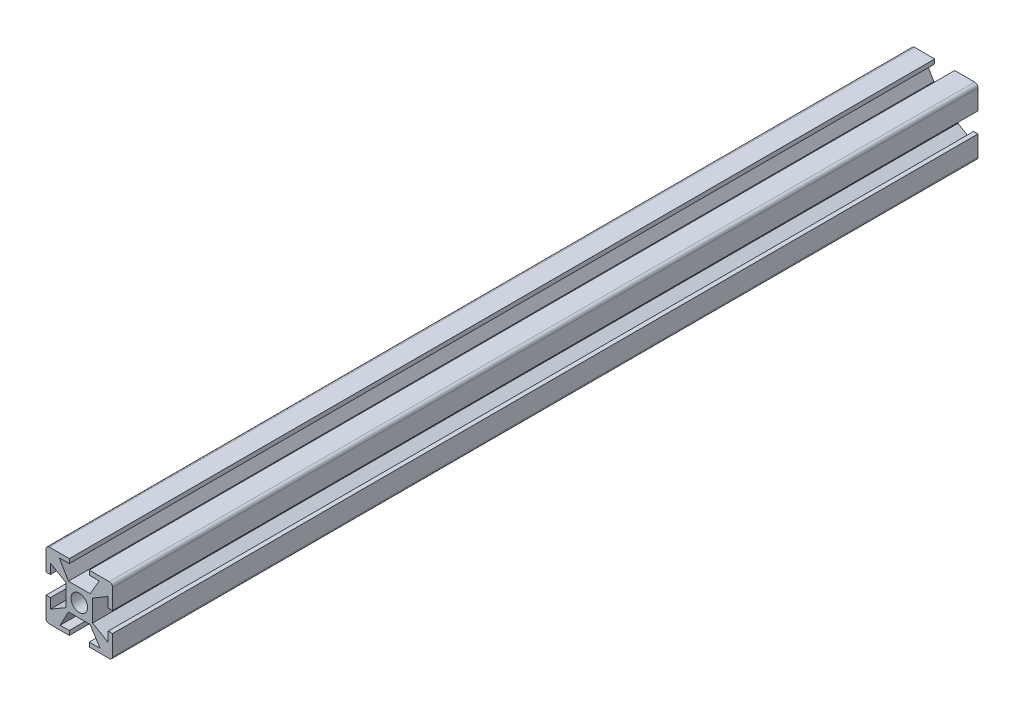
SolidWorks part; units mm, degrees
ref_plane "Alzado" through (0, 0, 0) normal (0, 0, 1) x (1, 0, 0)
ref_plane "Planta" through (0, 0, 0) normal (0, 1, 0) x (1, 0, 0)
ref_plane "Vista lateral" through (0, 0, 0) normal (1, 0, 0) x (0, 0, -1)
sketch "Croquis1" plane through (0, 0, 0) normal (0, 0, 1) x (1, 0, 0)
  line L0 (-3, 10) -> (3, 10)
  line L1 (-9, 10) -> (9, 10)
  line L2 (-10, 9) -> (-10, -9)
  line L3 (-9, -10) -> (9, -10)
  line L4 (10, 9) -> (10, -9)
  line L5 (-10, 10) -> (10, -10) construction
  line L6 (-10, -10) -> (10, 10) construction
  line L7 (-4, 4) -> (4, 4)
  line L8 (-4, 4) -> (-4, -4)
  line L9 (-4, -4) -> (4, -4)
  line L10 (4, 4) -> (4, -4)
  line L11 (-4, 4) -> (4, -4) construction
  line L12 (-4, -4) -> (4, 4) construction
  line L13 (3, 10) -> (3, 8.7)
  line L14 (-3.25, 4) -> (3.25, 4)
  line L15 (0, 10) -> (0, -10) construction
  line L16 (-10, 0) -> (10, 0) construction
  line L20 (-3, 10) -> (-3, 8.7)
  line L22 (3, -10) -> (3, -8.7)
  line L23 (-3, -10) -> (3, -10)
  line L24 (-3, -10) -> (-3, -8.7)
  line L25 (-5.75, -8.7) -> (-3, -8.7)
  line L26 (-5.75, -8.7) -> (-3.25, -4)
  line L27 (-3.25, -4) -> (3.25, -4)
  line L28 (6.25, -8.7) -> (3.25, -4)
  line L29 (3, -8.7) -> (6.25, -8.7)
  line L30 (-10, 3) -> (-10, -3)
  line L31 (-4, 3.25) -> (-4, -3.25)
  line L32 (-10, 3) -> (-8.7, 3)
  line L33 (-8.7, -6) -> (-8.7, -3)
  line L34 (-8.7, 6) -> (-4, 3.25)
  line L35 (-8.7, -6) -> (-4, -3.25)
  line L36 (-10, -3) -> (-8.7, -3)
  line L37 (-8.7, 3) -> (-8.7, 6)
  line L38 (8.7, -6) -> (4, -3.25)
  line L39 (4, 3.25) -> (4, -3.25)
  line L40 (8.7, 6) -> (4, 3.25)
  line L41 (8.7, 3) -> (8.7, 6)
  line L42 (10, 3) -> (8.7, 3)
  line L43 (10, 3) -> (10, -3)
  line L44 (10, -3) -> (8.7, -3)
  line L45 (8.7, -6) -> (8.7, -3)
  line L46 (-6, 8.7) -> (-3, 8.7)
  line L47 (-6, 8.7) -> (-3.25, 4)
  line L48 (6, 8.7) -> (3.25, 4)
  line L49 (3, 8.7) -> (6, 8.7)
  circle A0 centre (0, 0) radius 2.5
  arc A1 (-10, -9) -> (-9, -10) centre (-9, -9) ccw
  arc A2 (9, -10) -> (10, -9) centre (9, -9) ccw
  arc A3 (9, 10) -> (10, 9) centre (9, 9) cw
  arc A4 (-9, 10) -> (-10, 9) centre (-9, 9) ccw
  point P0 (0, 0)
  point P6 (0, 0)
  point P14 (0, 10)
  point P18 (0, 4)
  point P25 (0, 8.7)
  point P37 (-10, 0)
  point P40 (-4, 0)
  point P44 (-8.7, 0)
  point P56 (0, 8.7)
  dimension "D12" = 5
  dimension "D13" = 1
  dimension "D1" = 20
  dimension "D2" = 20
  dimension "D3" = 8
  dimension "D4" = 8
  dimension "D5" = 6
  dimension "D6" = 6.5
  dimension "D7" = 12
  dimension "D8" = 6.5
  dimension "D9" = 6
  dimension "D10" = 1.3
  dimension "D11" = 12
extrude "Saliente-Extruir4" add sketch "Croquis1" along normal blind 260 contours L1 A4 L2 L32 L37 L34 L8 L7 L47 L46 L20 | A3 L1 L13 L49 L48 L7 L10 L40 L41 L42 L4 | L3 A2 L4 L44 L45 L38 L10 L9 L28 L29 L22 | L2 A1 L3 L24 L25 L26 L9 L8 L35 L33 L36 | L10 L7 L8 L9 A0
